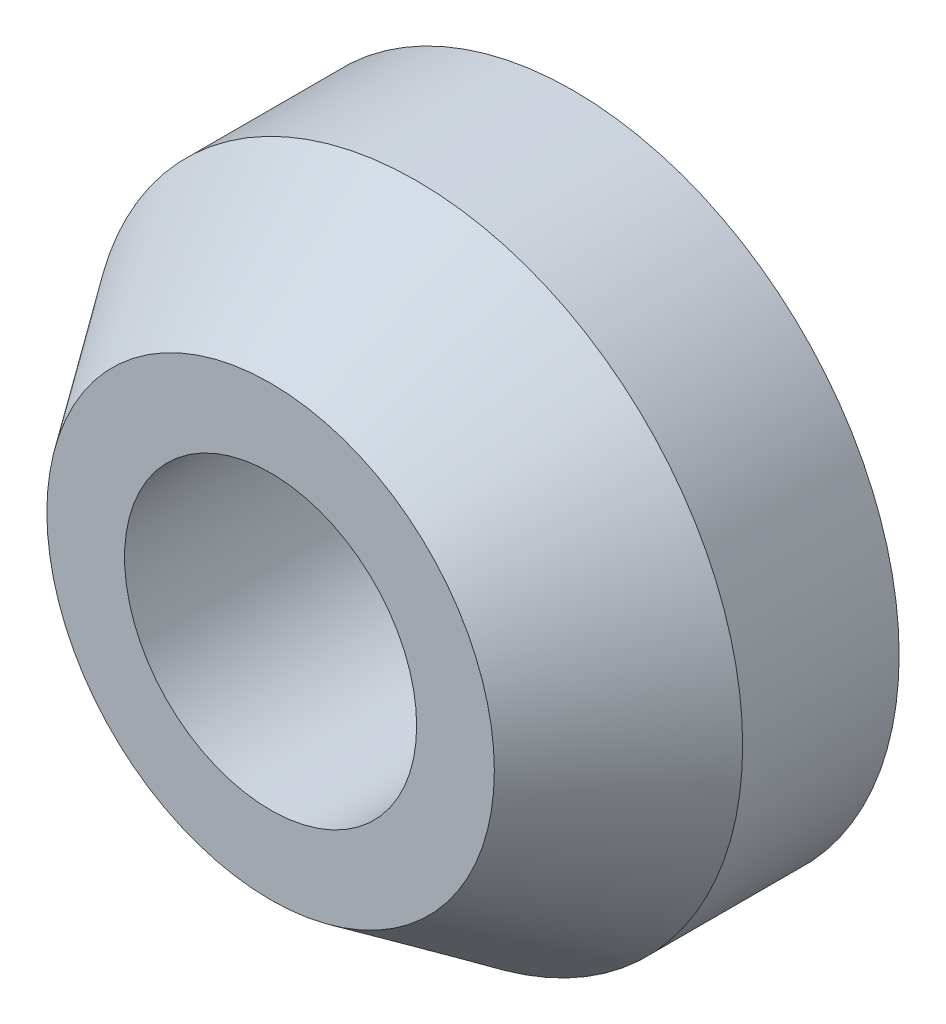
SolidWorks part; units mm, degrees
ref_plane "Front Plane" through (0, 0, 0) normal (0, 0, 1) x (1, 0, 0)
ref_plane "Top Plane" through (0, 0, 0) normal (0, 1, 0) x (1, 0, 0)
ref_plane "Right Plane" through (0, 0, 0) normal (1, 0, 0) x (0, 0, -1)
sketch "Sketch1" plane through (0, 0, 0) normal (0, 0, 1) x (1, 0, 0)
  circle A0 centre (0, 0) radius 3.175
extrude "Extrude1" add sketch "Sketch1" along normal blind 2.9464
sketch "Sketch2" plane through (0, 0, 2.9464) normal (0, 0, 1) x (1, 0, 0)
  circle A0 centre (0, 0) radius 1.4224
extrude "Extrude2" cut sketch "Sketch2" against normal through all
chamfer "Chamfer1" distance 1.4224 angle 35 1 edges at (3.175, 0, 2.9464)
